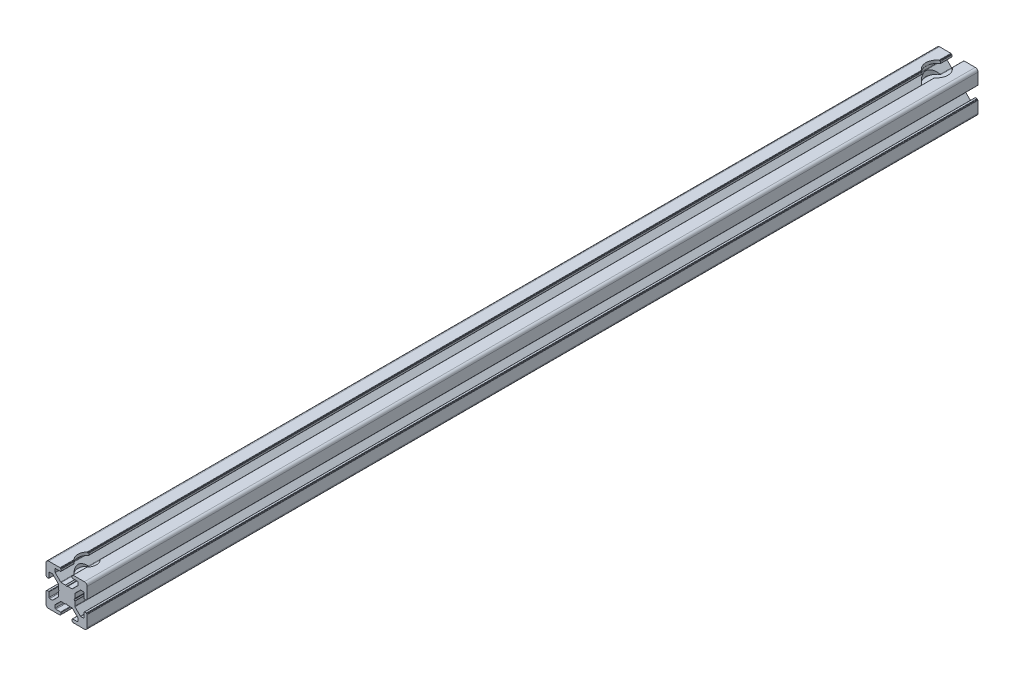
SolidWorks part; units mm, degrees
material "6061 Alloy"
ref_plane "Front Plane" through (0, 0, 0) normal (0, 0, 1) x (1, 0, 0)
ref_plane "Top Plane" through (0, 0, 0) normal (0, 1, 0) x (1, 0, 0)
ref_plane "Right Plane" through (0, 0, 0) normal (1, 0, 0) x (0, 0, -1)
sketch "Sketch1" plane through (0, 0, 0) normal (0, 0, 1) x (1, 0, 0)
  line B0 (-12.8, 4.4) -> (-12.8, 7.85)
  line B1 (-12.3, 8.35) -> (-10.3956, 8.35)
  line B2 (-10.042, 8.2036) -> (-6.1464, 4.308)
  line B3 (-6, 3.9544) -> (-6, 0.934)
  line B4 (-5.933, 0.684) -> (-5.5381, 0)
  line B5 (-5.5381, 0) -> (-5.933, -0.684)
  line B6 (-6, -0.934) -> (-6, -3.9544)
  line B7 (-6.1464, -4.308) -> (-10.042, -8.2036)
  line B8 (-10.3956, -8.35) -> (-12.3, -8.35)
  line B9 (-12.8, -7.85) -> (-12.8, -4.4)
  line B10 (-13.1, -4.1) -> (-14.3, -4.1)
  line B11 (-14.5, -4.3) -> (-14.5, -4.4)
  line B12 (-14.7, -4.6) -> (-14.8, -4.6)
  line B13 (-15, -4.8) -> (-15, -13)
  line B14 (-13, -15) -> (-4.8, -15)
  line B15 (-4.6, -14.8) -> (-4.6, -14.7)
  line B16 (-4.4, -14.5) -> (-4.3, -14.5)
  line B17 (-4.1, -14.3) -> (-4.1, -13.1)
  line B18 (-4.4, -12.8) -> (-7.85, -12.8)
  line B19 (-8.35, -12.3) -> (-8.35, -10.3956)
  line B20 (-8.2036, -10.042) -> (-4.308, -6.1464)
  line B21 (-3.9544, -6) -> (-0.934, -6)
  line B22 (-0.684, -5.933) -> (0, -5.5381)
  line B23 (0, -5.5381) -> (0.684, -5.933)
  line B24 (0.934, -6) -> (3.9544, -6)
  line B25 (4.308, -6.1464) -> (8.2036, -10.042)
  line B26 (8.35, -10.3956) -> (8.35, -12.3)
  line B27 (7.85, -12.8) -> (4.4, -12.8)
  line B28 (4.1, -13.1) -> (4.1, -14.3)
  line B29 (4.3, -14.5) -> (4.4, -14.5)
  line B30 (4.6, -14.7) -> (4.6, -14.8)
  line B31 (4.8, -15) -> (13, -15)
  line B32 (15, -13) -> (15, -4.8)
  line B33 (14.8, -4.6) -> (14.7, -4.6)
  line B34 (14.5, -4.4) -> (14.5, -4.3)
  line B35 (14.3, -4.1) -> (13.1, -4.1)
  line B36 (12.8, -4.4) -> (12.8, -7.85)
  line B37 (12.3, -8.35) -> (10.3956, -8.35)
  line B38 (10.042, -8.2036) -> (6.1464, -4.308)
  line B39 (6, -3.9544) -> (6, -0.934)
  line B40 (5.933, -0.684) -> (5.5381, 0)
  line B41 (5.5381, 0) -> (5.933, 0.684)
  line B42 (6, 0.934) -> (6, 3.9544)
  line B43 (6.1464, 4.308) -> (10.042, 8.2036)
  line B44 (10.3956, 8.35) -> (12.3, 8.35)
  line B45 (12.8, 7.85) -> (12.8, 4.4)
  line B46 (13.1, 4.1) -> (14.3, 4.1)
  line B47 (14.5, 4.3) -> (14.5, 4.4)
  line B48 (14.7, 4.6) -> (14.8, 4.6)
  line B49 (15, 4.8) -> (15, 13)
  line B50 (13, 15) -> (4.8, 15)
  line B51 (4.6, 14.8) -> (4.6, 14.7)
  line B52 (4.4, 14.5) -> (4.3, 14.5)
  line B53 (4.1, 14.3) -> (4.1, 13.1)
  line B54 (4.4, 12.8) -> (7.85, 12.8)
  line B55 (8.35, 12.3) -> (8.35, 10.3956)
  line B56 (8.2036, 10.042) -> (4.308, 6.1464)
  line B57 (3.9544, 6) -> (0.934, 6)
  line B58 (0.684, 5.933) -> (0, 5.5381)
  line B59 (0, 5.5381) -> (-0.684, 5.933)
  line B60 (-0.934, 6) -> (-3.9544, 6)
  line B61 (-4.308, 6.1464) -> (-8.2036, 10.042)
  line B62 (-8.35, 10.3956) -> (-8.35, 12.3)
  line B63 (-7.85, 12.8) -> (-4.4, 12.8)
  line B64 (-4.1, 13.1) -> (-4.1, 14.3)
  line B65 (-4.3, 14.5) -> (-4.4, 14.5)
  line B66 (-4.6, 14.7) -> (-4.6, 14.8)
  line B67 (-4.8, 15) -> (-13, 15)
  line B68 (-15, 13) -> (-15, 4.8)
  line B69 (-14.8, 4.6) -> (-14.7, 4.6)
  line B70 (-14.5, 4.4) -> (-14.5, 4.3)
  line B71 (-14.3, 4.1) -> (-13.1, 4.1)
  arc B72 (-13.1, 4.1) -> (-12.8, 4.4) centre (-13.1, 4.4) ccw
  arc B73 (-12.3, 8.35) -> (-12.8, 7.85) centre (-12.3, 7.85) ccw
  arc B74 (-10.042, 8.2036) -> (-10.3956, 8.35) centre (-10.3956, 7.85) ccw
  arc B75 (-6, 3.9544) -> (-6.1464, 4.308) centre (-6.5, 3.9544) ccw
  arc B76 (-6, 0.934) -> (-5.933, 0.684) centre (-5.5, 0.934) ccw
  arc B77 (-5.933, -0.684) -> (-6, -0.934) centre (-5.5, -0.934) ccw
  arc B78 (-6.1464, -4.308) -> (-6, -3.9544) centre (-6.5, -3.9544) ccw
  arc B79 (-10.3956, -8.35) -> (-10.042, -8.2036) centre (-10.3956, -7.85) ccw
  arc B80 (-12.8, -7.85) -> (-12.3, -8.35) centre (-12.3, -7.85) ccw
  arc B81 (-12.8, -4.4) -> (-13.1, -4.1) centre (-13.1, -4.4) ccw
  arc B82 (-14.3, -4.1) -> (-14.5, -4.3) centre (-14.3, -4.3) ccw
  arc B83 (-14.7, -4.6) -> (-14.5, -4.4) centre (-14.7, -4.4) ccw
  arc B84 (-14.8, -4.6) -> (-15, -4.8) centre (-14.8, -4.8) ccw
  arc B85 (-15, -13) -> (-13, -15) centre (-13, -13) ccw
  arc B86 (-4.8, -15) -> (-4.6, -14.8) centre (-4.8, -14.8) ccw
  arc B87 (-4.4, -14.5) -> (-4.6, -14.7) centre (-4.4, -14.7) ccw
  arc B88 (-4.3, -14.5) -> (-4.1, -14.3) centre (-4.3, -14.3) ccw
  arc B89 (-4.1, -13.1) -> (-4.4, -12.8) centre (-4.4, -13.1) ccw
  arc B90 (-8.35, -12.3) -> (-7.85, -12.8) centre (-7.85, -12.3) ccw
  arc B91 (-8.2036, -10.042) -> (-8.35, -10.3956) centre (-7.85, -10.3956) ccw
  arc B92 (-3.9544, -6) -> (-4.308, -6.1464) centre (-3.9544, -6.5) ccw
  arc B93 (-0.934, -6) -> (-0.684, -5.933) centre (-0.934, -5.5) ccw
  arc B94 (0.684, -5.933) -> (0.934, -6) centre (0.934, -5.5) ccw
  arc B95 (4.308, -6.1464) -> (3.9544, -6) centre (3.9544, -6.5) ccw
  arc B96 (8.35, -10.3956) -> (8.2036, -10.042) centre (7.85, -10.3956) ccw
  arc B97 (7.85, -12.8) -> (8.35, -12.3) centre (7.85, -12.3) ccw
  arc B98 (4.4, -12.8) -> (4.1, -13.1) centre (4.4, -13.1) ccw
  arc B99 (4.1, -14.3) -> (4.3, -14.5) centre (4.3, -14.3) ccw
  arc B100 (4.6, -14.7) -> (4.4, -14.5) centre (4.4, -14.7) ccw
  arc B101 (4.6, -14.8) -> (4.8, -15) centre (4.8, -14.8) ccw
  arc B102 (13, -15) -> (15, -13) centre (13, -13) ccw
  arc B103 (15, -4.8) -> (14.8, -4.6) centre (14.8, -4.8) ccw
  arc B104 (14.5, -4.4) -> (14.7, -4.6) centre (14.7, -4.4) ccw
  arc B105 (14.5, -4.3) -> (14.3, -4.1) centre (14.3, -4.3) ccw
  arc B106 (13.1, -4.1) -> (12.8, -4.4) centre (13.1, -4.4) ccw
  arc B107 (12.3, -8.35) -> (12.8, -7.85) centre (12.3, -7.85) ccw
  arc B108 (10.042, -8.2036) -> (10.3956, -8.35) centre (10.3956, -7.85) ccw
  arc B109 (6, -3.9544) -> (6.1464, -4.308) centre (6.5, -3.9544) ccw
  arc B110 (6, -0.934) -> (5.933, -0.684) centre (5.5, -0.934) ccw
  arc B111 (5.933, 0.684) -> (6, 0.934) centre (5.5, 0.934) ccw
  arc B112 (6.1464, 4.308) -> (6, 3.9544) centre (6.5, 3.9544) ccw
  arc B113 (10.3956, 8.35) -> (10.042, 8.2036) centre (10.3956, 7.85) ccw
  arc B114 (12.8, 7.85) -> (12.3, 8.35) centre (12.3, 7.85) ccw
  arc B115 (12.8, 4.4) -> (13.1, 4.1) centre (13.1, 4.4) ccw
  arc B116 (14.3, 4.1) -> (14.5, 4.3) centre (14.3, 4.3) ccw
  arc B117 (14.7, 4.6) -> (14.5, 4.4) centre (14.7, 4.4) ccw
  arc B118 (14.8, 4.6) -> (15, 4.8) centre (14.8, 4.8) ccw
  arc B119 (15, 13) -> (13, 15) centre (13, 13) ccw
  arc B120 (4.8, 15) -> (4.6, 14.8) centre (4.8, 14.8) ccw
  arc B121 (4.4, 14.5) -> (4.6, 14.7) centre (4.4, 14.7) ccw
  arc B122 (4.3, 14.5) -> (4.1, 14.3) centre (4.3, 14.3) ccw
  arc B123 (4.1, 13.1) -> (4.4, 12.8) centre (4.4, 13.1) ccw
  arc B124 (8.35, 12.3) -> (7.85, 12.8) centre (7.85, 12.3) ccw
  arc B125 (8.2036, 10.042) -> (8.35, 10.3956) centre (7.85, 10.3956) ccw
  arc B126 (3.9544, 6) -> (4.308, 6.1464) centre (3.9544, 6.5) ccw
  arc B127 (0.934, 6) -> (0.684, 5.933) centre (0.934, 5.5) ccw
  arc B128 (-0.684, 5.933) -> (-0.934, 6) centre (-0.934, 5.5) ccw
  arc B129 (-4.308, 6.1464) -> (-3.9544, 6) centre (-3.9544, 6.5) ccw
  arc B130 (-8.35, 10.3956) -> (-8.2036, 10.042) centre (-7.85, 10.3956) ccw
  arc B131 (-7.85, 12.8) -> (-8.35, 12.3) centre (-7.85, 12.3) ccw
  arc B132 (-4.4, 12.8) -> (-4.1, 13.1) centre (-4.4, 13.1) ccw
  arc B133 (-4.1, 14.3) -> (-4.3, 14.5) centre (-4.3, 14.3) ccw
  arc B134 (-4.6, 14.7) -> (-4.4, 14.5) centre (-4.4, 14.7) ccw
  arc B135 (-4.6, 14.8) -> (-4.8, 15) centre (-4.8, 14.8) ccw
  arc B136 (-13, 15) -> (-15, 13) centre (-13, 13) ccw
  arc B137 (-15, 4.8) -> (-14.8, 4.6) centre (-14.8, 4.8) ccw
  arc B138 (-14.5, 4.4) -> (-14.7, 4.6) centre (-14.7, 4.4) ccw
  arc B139 (-14.5, 4.3) -> (-14.3, 4.1) centre (-14.3, 4.3) ccw
sketch_block_instance "Frame30-1"
sketch_block "Frame30"
extrude "Boss-Extrude1" add sketch "Sketch1" along normal blind 650
sketch "Sketch2" plane through (0, 15, 0) normal (0, 1, 0) x (1, 0, 0)
  line L0 (0, -650) -> (0, 0) construction
  line L1 (3.9544, -650) -> (0.934, -650) construction
  line L2 (3.9544, 0) -> (0.934, 0) construction
  circle A0 centre (0, -15) radius 4
  circle A1 centre (0, -635) radius 4
  dimension "D1" = 8
  dimension "D3" = 8
  dimension "D2" = 15
  dimension "D4" = 15
extrude "Cut-Extrude1" cut sketch "Sketch2" against normal through all
sketch "Sketch3" plane through (0, 15, 0) normal (0, 1, 0) x (1, 0, 0)
  circle A0 centre (0, -15) radius 8
  circle A1 centre (0, -635) radius 6.7358
  dimension "D1" = 16
extrude "Cut-Extrude2" cut sketch "Sketch3" against normal blind 9
